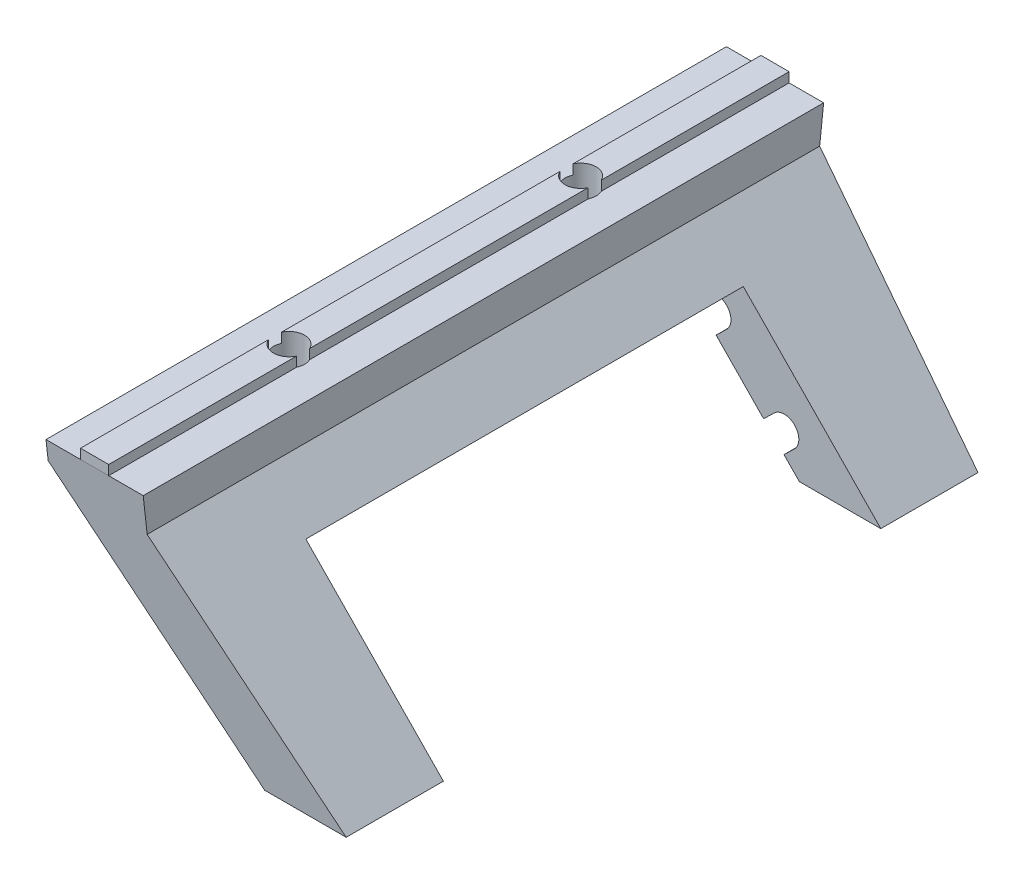
SolidWorks part; units mm, degrees
ref_plane "Front Plane" through (0, 0, 0) normal (0, 0, 1) x (1, 0, 0)
ref_plane "Top Plane" through (0, 0, 0) normal (0, 1, 0) x (1, 0, 0)
ref_plane "Right Plane" through (0, 0, 0) normal (1, 0, 0) x (0, 0, -1)
sketch "Sketch1" plane through (0, 0, 0) normal (0, 0, 1) x (1, 0, 0)
  line L0 (-10, 22.5) -> (-10, 18.842)
  line L1 (-20, 20.5) -> (-20, 22.5)
  line L2 (-10, 18.842) -> (8.3824, 0)
  line L3 (8.3824, 0) -> (0, 0)
  line L4 (0, 0) -> (-20, 20.5)
  line L5 (-20, 22.5) -> (-16.45, 22.5)
  line L6 (-16.45, 22.5) -> (-16.45, 23.5)
  line L7 (-16.45, 23.5) -> (-13.55, 23.5)
  line L8 (-13.55, 23.5) -> (-13.55, 22.5)
  line L9 (-13.55, 22.5) -> (-10, 22.5)
  line L10 (8.3824, 0) -> (34.2968, 0) construction
  point P0 (-20, 20.5471)
  dimension "D1" = 10
  dimension "D2" = 2.9
  dimension "D3" = 2
  dimension "D4" = 20
  dimension "D5" = 6
  dimension "D6" = 22.5
  dimension "D7" = 1
extrude "Main" add sketch "Sketch1" along normal mid plane 70
sketch "Sketch2" plane through (0, 12.0711, 0) normal (1, 0, 0) x (0, 0, 1)
  line L0 (-35, -10.4289) -> (-32.5, 12.0711)
  line L2 (-35, -8.4289) -> (-35, 12.0711) construction
  line L3 (35, 12.0711) -> (-35, 12.0711) construction
  line L4 (35, -10.4289) -> (-35, -10.4289) construction
  line L5 (-35, 12.0711) -> (-35, -10.4289)
  line L6 (35, -10.4289) -> (35, 12.0711)
  line L7 (35, -10.4289) -> (-35, -10.4289) construction
  line L8 (32.5, 12.0711) -> (35, -10.4289)
  line L15 (-32.5, 12.0711) -> (-35, 12.0711)
  line L16 (32.5, 12.0711) -> (35, 12.0711)
  point P1 (-35, -10.4289)
  point P2 (35, -10.4289)
  point P3 (-35, -10.4289)
  dimension "D2" = 65
  dimension "D5" = 2.5
extrude "SideCut" cut sketch "Sketch2" against normal through all and the other way through all
sketch "Sketch5" plane through (0, 0, 0) normal (1, 0, 0) x (0, 0, 1)
  line L1 (-22.5, 45.5) -> (22.5, 45.5)
  line L2 (-22.5, 45.5) -> (-22.5, -14.5)
  line L3 (-22.5, -14.5) -> (22.5, -14.5)
  line L4 (22.5, 45.5) -> (22.5, -14.5)
  line L6 (0, -55) -> (0, 55) construction
  line L8 (35, -22.5) -> (-35, -22.5) construction
  point P4 (-22.5, -4.6467)
  point P8 (0, 45.5)
  dimension "D1" = 60
  dimension "D2" = 8
  dimension "D3" = 45
extrude "CentralCut" cut sketch "Sketch5" against normal through all both and the other way through all
sketch "Sketch3" plane through (0, 23.5, 0) normal (0, 1, 0) x (1, 0, 0)
  line L6 (-20, -35) -> (-20, 35) construction
  circle A0 centre (-15, 15) radius 1.6
  circle A1 centre (-15, -15) radius 1.6
  point P4 (0, 0)
  dimension "D1" = 3.2
  dimension "D2" = 5
  dimension "D3" = 15
  dimension "D4" = 15
extrude "MakerBeamFixHoles" cut sketch "Sketch3" against normal through all and the other way through all
sketch "Sketch4" plane through (0, 0, 0) normal (0, 0, 1) x (1, 0, 0)
  line L0 (-10.6547, 10.9211) -> (-8.5598, 8.7737)
  line L1 (-8.5598, 8.7737) -> (-7.4861, 9.8212)
  line L3 (-10, 18.842) -> (8.3824, 0) construction
  line L4 (-10.6547, 10.9211) -> (-9.581, 11.9686)
  line L5 (-20, 20.5) -> (0, 0) construction
  arc A0 (-7.4861, 9.8212) -> (-9.581, 11.9686) centre (-8.5336, 10.8949) ccw
  dimension "D1" = 1.5
  dimension "D2" = 1.5
  dimension "D3" = 5
extrude "RollerSupportHoles" cut sketch "Sketch4" against normal mid plane 60
pattern_linear "LPattern1" count 3 spacing 10 along (0.6983, -0.7158, 0) of "RollerSupportHoles"
sketch "Sketch6" plane through (0, 14.5, 0) normal (0, -1, 0) x (-1, 0, 0)
  circle A0 centre (15, 15) radius 4.25
  circle A2 centre (15, 15) radius 1.6 construction
  circle A3 centre (15, -15) radius 4.25
  circle A4 centre (15, -15) radius 1.6 construction
  point P6 (0, 0)
  dimension "D1" = 8.5
extrude "ScrewHole" cut sketch "Sketch6" against normal blind 3
